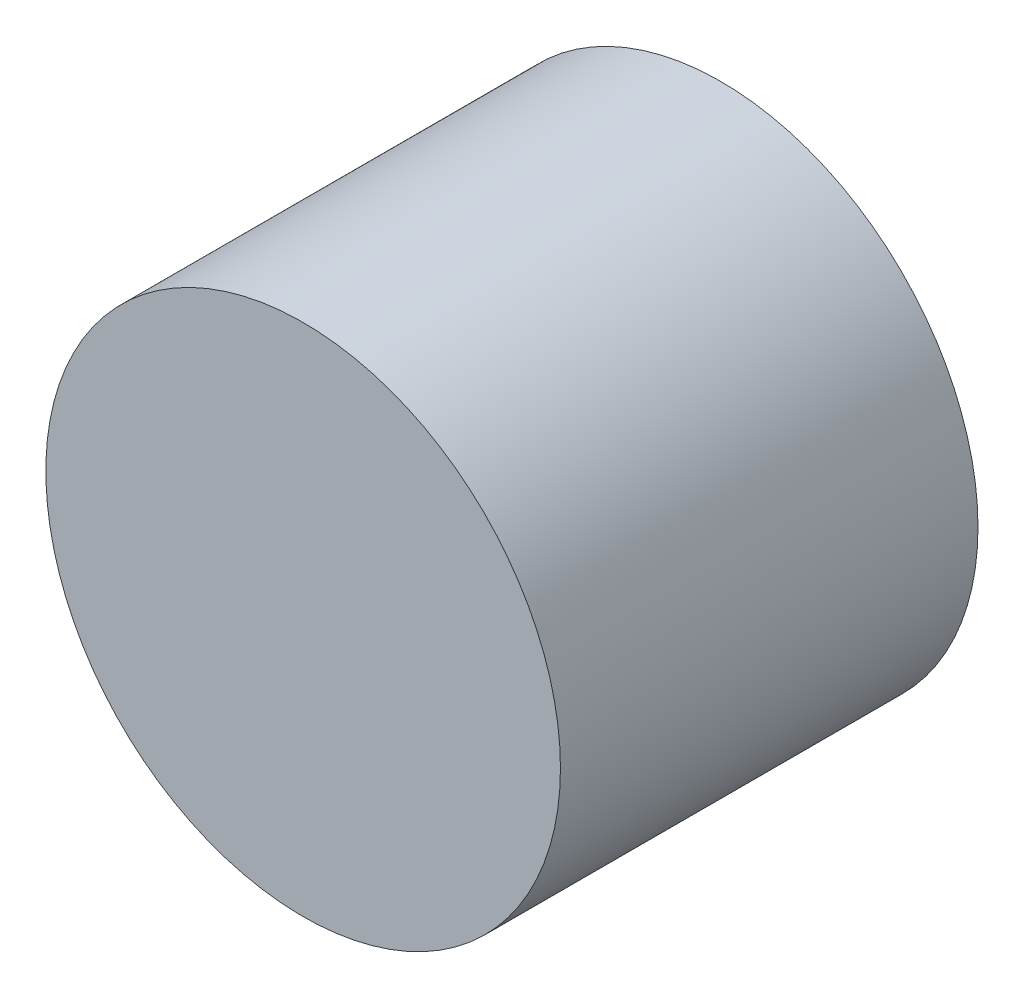
SolidWorks part; units mm, degrees
ref_plane "前视基准面" through (0, 0, 0) normal (0, 0, 1) x (1, 0, 0)
ref_plane "上视基准面" through (0, 0, 0) normal (0, 1, 0) x (1, 0, 0)
ref_plane "右视基准面" through (0, 0, 0) normal (1, 0, 0) x (0, 0, -1)
other "Configuration Table"
sketch "草图1" plane through (0, 0, 0) normal (0, 0, 1) x (1, 0, 0)
  line L0 (12.5339, 23.8842) -> (19.3853, 21.6176)
  line L1 (21.8778, 17.5267) -> (17.5332, -9.9373)
  line L2 (-14.2802, 23.9348) -> (12.2198, 23.9348)
  line L3 (-23.6314, 17.5267) -> (-19.2868, -9.9373)
  line L4 (-21.1875, 21.6011) -> (-14.6074, 23.8797)
  line L5 (-13.6568, -14.7467) -> (11.9032, -14.7467)
  arc A0 (21.8778, 17.5267) -> (19.3853, 21.6176) centre (18.2232, 18.1048) ccw
  arc A1 (12.5339, 23.8842) -> (12.2198, 23.9348) centre (12.2198, 22.9348) ccw
  arc A2 (11.9032, -14.7467) -> (17.5332, -9.9373) centre (11.9032, -9.0467) ccw
  arc A3 (-19.2868, -9.9373) -> (-13.6568, -14.7467) centre (-13.6568, -9.0467) ccw
  arc A4 (-21.1875, 21.6011) -> (-23.6314, 17.5267) centre (-19.9768, 18.1048) ccw
  arc A5 (-14.2802, 23.9348) -> (-14.6074, 23.8797) centre (-14.2802, 22.9348) ccw
  circle A6 centre (-17.5162, 20.5985) radius 1.2325
  dimension "D1" = 7.4
  dimension "D2" = 11.4
extrude "凸台-拉伸1" add sketch "草图1" along normal blind 2 contours A6
sketch "草图2" plane through (0, 0, 0) normal (0, 0, 1) x (1, 0, 0)
  line L0 (12.5339, 23.8842) -> (19.3853, 21.6176)
  line L1 (21.8778, 17.5267) -> (17.5332, -9.9373)
  line L2 (-14.2802, 23.9348) -> (12.2198, 23.9348)
  line L3 (-23.6314, 17.5267) -> (-19.2868, -9.9373)
  line L4 (-21.1875, 21.6011) -> (-14.6074, 23.8797)
  line L5 (-13.6568, -14.7467) -> (11.9032, -14.7467)
  arc A0 (21.8778, 17.5267) -> (19.3853, 21.6176) centre (18.2232, 18.1048) ccw
  arc A1 (12.5339, 23.8842) -> (12.2198, 23.9348) centre (12.2198, 22.9348) ccw
  arc A2 (11.9032, -14.7467) -> (17.5332, -9.9373) centre (11.9032, -9.0467) ccw
  arc A3 (-19.2868, -9.9373) -> (-13.6568, -14.7467) centre (-13.6568, -9.0467) ccw
  arc A4 (-21.1875, 21.6011) -> (-23.6314, 17.5267) centre (-19.9768, 18.1048) ccw
  arc A5 (-14.2802, 23.9348) -> (-14.6074, 23.8797) centre (-14.2802, 22.9348) ccw
  dimension "D1" = 7.4
  dimension "D2" = 11.4
pattern_curve "曲线阵列1" of "凸台-拉伸1" parameters "D1"=2, "D3"=50, "D2"=1, "D4"=50
curve "组合曲线1"
